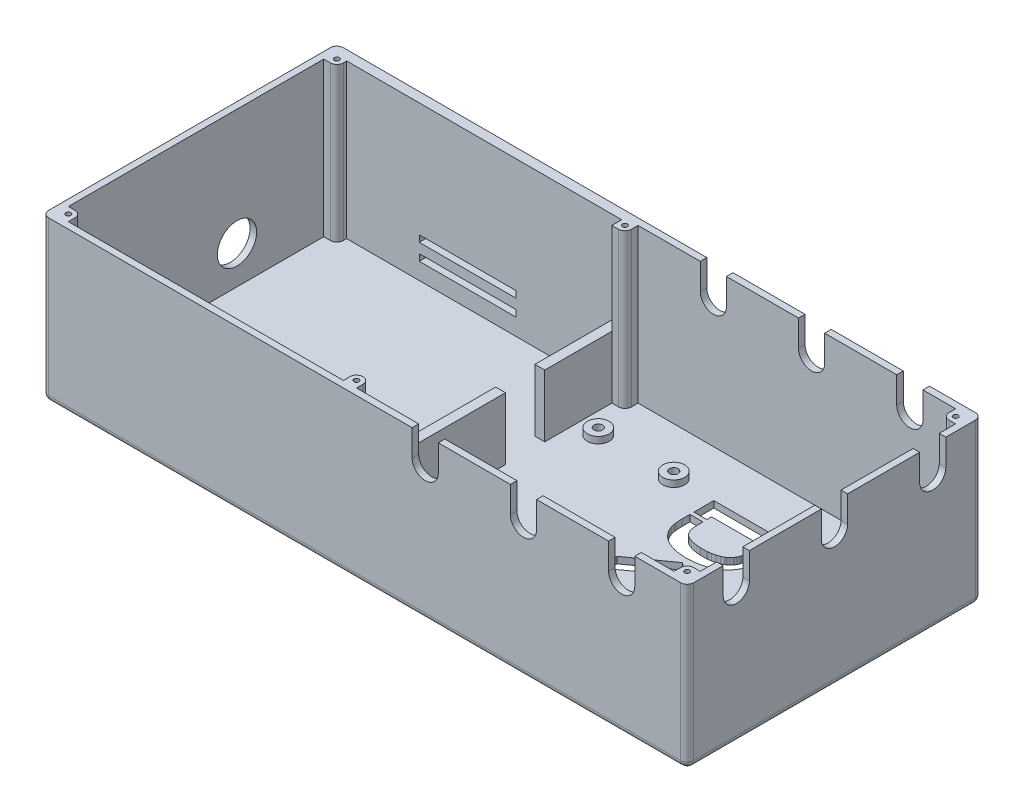
SolidWorks part; units mm, degrees
ref_plane "Front Plane" through (0, 0, 0) normal (0, 0, 1) x (1, 0, 0)
ref_plane "Top Plane" through (0, 0, 0) normal (0, 1, 0) x (1, 0, 0)
ref_plane "Right Plane" through (0, 0, 0) normal (1, 0, 0) x (0, 0, -1)
sketch "Sketch2" plane through (0, 0, 0) normal (0, 1, 0) x (1, 0, 0)
  line L1 (0, 0) -> (197, 0)
  line L2 (0, 0) -> (0, 90)
  line L3 (0, 90) -> (197, 90)
  line L4 (197, 0) -> (197, 90)
  dimension "D1" = 197
  dimension "D2" = 90
extrude "Boss-Extrude1" add sketch "Sketch2" along normal blind 21
shell "Shell1" thickness 2
sketch "Sketch3" plane through (0.4867, 2, 38.6702) normal (0, 1, 0) x (1, 0, 0)
  circle A0 centre (118.949, 112.1395) radius 1.325
  circle A1 centre (118.949, 54.0895) radius 3.325
  circle A2 centre (95.899, 54.0895) radius 3.325
  circle A3 centre (95.899, 112.1395) radius 3.325
  circle A4 centre (118.949, 112.1395) radius 3.325
  circle A5 centre (95.899, 112.1395) radius 1.325
  circle A6 centre (95.899, 54.0895) radius 1.325
  circle A7 centre (118.949, 54.0895) radius 1.325
extrude "Boss-Extrude2" add sketch "Sketch3" along normal blind 2
sketch "Sketch6" plane through (0, 2, 0) normal (0, 1, 0) x (1, 0, 0)
  circle A0 centre (119.4356, 73.4693) radius 1.325 construction
  circle A1 centre (96.3856, 73.4693) radius 1.325
  circle A2 centre (96.3856, 73.4693) radius 1.325
  circle A3 centre (119.4356, 15.4193) radius 1.325 construction
  circle A4 centre (96.3856, 15.4193) radius 1.325 construction
  circle A5 centre (119.4356, 73.4693) radius 1.325
  circle A6 centre (119.4356, 15.4193) radius 1.325
  circle A7 centre (96.3856, 15.4193) radius 1.325
  dimension "D1" = 0
extrude "Cut-Extrude2" cut sketch "Sketch6" against normal through all
sketch "Sketch7" plane through (0, 0, 0) normal (-1, 0, 0) x (0, 0, 1)
  line L1 (-90, 10.5) -> (-83.6201, 10.5) construction
  line L2 (-90, 21) -> (-90, 0) construction
  circle A0 centre (-57.5, 13.5) radius 6
  dimension "D1" = 12
  dimension "D2" = 3
  dimension "D3" = 32.5
sketch "Sketch8" plane through (0, 2, 0) normal (0, 1, 0) x (1, 0, 0)
  line L0 (2, 88) -> (2, 2) construction
  line L1 (2, 28) -> (87, 28)
  line L2 (2, 45) -> (15.4419, 45) construction
  line L3 (2, 87) -> (87, 87)
  line L4 (87, 28) -> (87, 87)
  line L5 (2, 88) -> (2, 2) construction
  line L7 (2, 25) -> (90, 25)
  line L8 (90, 25) -> (90, 90)
  line L9 (2, 90) -> (90, 90)
  line L10 (2, 25) -> (2, 28)
  line L11 (2, 87) -> (2, 90)
  line L12 (197, 90) -> (0, 90) construction
  dimension "D1" = 59
  dimension "D2" = 0
  dimension "D3" = 85
  dimension "D4" = 3
extrude "Boss-Extrude3" add sketch "Sketch8" along normal up to surface (19 mm away) up to face at (98.5, 21, -45)
sketch "Sketch10" plane through (0, 21, 0) normal (0, 1, 0) x (1, 0, 0)
  line L0 (87, 57.5) -> (90, 57.5) construction
  line L2 (90, 25) -> (90, 88) construction
  line L3 (87, 87) -> (87, 28) construction
  line L4 (87, 51.5) -> (90, 51.5)
  line L5 (87, 51.5) -> (87, 63.5)
  line L6 (87, 63.5) -> (90, 63.5)
  line L7 (90, 51.5) -> (90, 63.5)
  line L8 (87, 28) -> (87, 87) construction
  line L9 (90, 25) -> (90, 88) construction
  dimension "D1" = 12
  dimension "D2" = 6
extrude "Cut-Extrude5" cut sketch "Sketch10" against normal up to surface (19 mm away) up to face at (119.4356, 2, -18.7443)
sketch "Sketch12" plane through (0, 0, -75) normal (0, 0, -1) x (-1, 0, 0)
  line L1 (-57.7754, 12.1097) -> (-28.1833, 12.1097)
  line L2 (-57.7754, 12.1097) -> (-57.7754, 14.1097)
  line L3 (-57.7754, 14.1097) -> (-28.1833, 14.1097)
  line L4 (-28.1833, 12.1097) -> (-28.1833, 14.1097)
  line L5 (-57.7754, 7.1097) -> (-28.1833, 7.1097)
  line L6 (-57.7754, 7.1097) -> (-57.7754, 9.1097)
  line L7 (-57.7754, 9.1097) -> (-28.1833, 9.1097)
  line L8 (-28.1833, 7.1097) -> (-28.1833, 9.1097)
  dimension "D1" = 2
  dimension "D2" = 2
  dimension "D3" = 3
extrude "Cut-Extrude6" cut sketch "Sketch12" against normal up to surface (73 mm away) and the other way blind 67.0442 up to face at (98.5, 11.5, -2)
sketch "Sketch16" plane through (197, 0, 0) normal (1, 0, 0) x (0, 0, -1)
  line L0 (45, 21) -> (45, 0) construction
  line L1 (0, 21) -> (90, 21) construction
  line L2 (0, 0) -> (90, 0) construction
  line L3 (48, 14.2355) -> (48, 21)
  line L4 (48, 21) -> (42, 21)
  line L5 (42, 21) -> (42, 14.2355)
  arc A0 (42, 14.2355) -> (48, 14.2355) centre (45, 14.2355) ccw
  dimension "D1" = 6
extrude "Cut-Extrude8" cut sketch "Sketch16" against normal blind 10
fillet "Fillet1" radius 2 8 edges at (0, 10.5, -90) (197, 10.5, -90) (197, 10.5, 0) (197, 0, -45) (98.5, 0, -90) (0, 0, -45) (98.5, 0, 0) (0, 10.5, 0)
extrude "Cut-Extrude9" cut sketch "Sketch7" against normal blind 10
sketch "Sketch17" plane through (0, 21, 0) normal (0, 1, 0) x (1, 0, 0)
  line L0 (197, 48) -> (197, 42)
  line L22 (195, 90) -> (2, 90)
  line L23 (0, 88) -> (0, 2)
  line L24 (2, 0) -> (195, 0)
  line L25 (197, 2) -> (197, 42)
  line L27 (197, 42) -> (195, 42)
  line L28 (195, 42) -> (195, 2)
  line L29 (195, 2) -> (2, 2)
  line L30 (2, 2) -> (2, 25)
  line L31 (2, 25) -> (90, 25)
  line L32 (90, 25) -> (90, 51.5)
  line L33 (90, 51.5) -> (87, 51.5)
  line L34 (87, 51.5) -> (87, 28)
  line L35 (87, 28) -> (2, 28)
  line L36 (2, 28) -> (2, 87)
  line L37 (2, 87) -> (87, 87)
  line L38 (87, 87) -> (87, 63.5)
  line L39 (87, 63.5) -> (90, 63.5)
  line L40 (90, 63.5) -> (90, 88)
  line L41 (90, 88) -> (195, 88)
  line L42 (195, 88) -> (195, 48)
  line L43 (195, 48) -> (197, 48)
  line L44 (195, 90) -> (2, 90)
  line L45 (0, 88) -> (0, 2)
  line L46 (2, 0) -> (195, 0)
  line L47 (197, 2) -> (197, 42)
  line L48 (197, 48) -> (197, 88)
  line L49 (197, 48) -> (197, 88)
  arc A4 (2, 90) -> (0, 88) centre (2, 88) ccw
  arc A5 (0, 2) -> (2, 0) centre (2, 2) ccw
  arc A6 (195, 0) -> (197, 2) centre (195, 2) ccw
  arc A7 (197, 88) -> (195, 90) centre (195, 88) ccw
  arc A8 (2, 90) -> (0, 88) centre (2, 88) ccw
  arc A9 (0, 2) -> (2, 0) centre (2, 2) ccw
  arc A10 (195, 0) -> (197, 2) centre (195, 2) ccw
  arc A11 (197, 88) -> (195, 90) centre (195, 88) ccw
  dimension "D1" = 0
extrude "Boss-Extrude4" add sketch "Sketch17" along normal blind 24
sketch "Sketch18" plane through (0, 45, 0) normal (0, 1, 0) x (1, 0, 0)
  line L8 (194, 87) -> (3, 87)
  line L9 (3, 87) -> (3, 3)
  line L10 (3, 3) -> (194, 3)
  line L11 (194, 3) -> (194, 87)
  line L12 (194, 87) -> (3, 87)
  line L13 (3, 87) -> (3, 3)
  line L14 (3, 3) -> (194, 3)
  line L15 (194, 3) -> (194, 87)
  dimension "D1" = 3
extrude "Cut-Extrude10" cut sketch "Sketch18" against normal offset from surface (21 mm away) 3 up to face at (105, 21, -48.3333)
sketch "Sketch19" plane through (0, 2, 0) normal (0, 1, 0) x (1, 0, 0)
  line L0 (193, 88) -> (195, 88)
  line L1 (195, 88) -> (195, 84)
  line L2 (191, 86) -> (191, 88)
  line L3 (2, 2) -> (195, 2) construction
  line L4 (2, 25) -> (2, 2) construction
  line L5 (2, 2) -> (2, 88) construction
  line L6 (195, 90) -> (2, 90) construction
  line L7 (195, 2) -> (195, 88) construction
  line L8 (90, 63.5) -> (90, 88) construction
  line L9 (193, 84) -> (195, 84)
  line L10 (195, 88) -> (90, 88) construction
  line L11 (194, 45) -> (197, 45) construction
  line L12 (194, 3) -> (194, 87) construction
  line L13 (197, 2) -> (197, 88) construction
  line L14 (191, 2) -> (193, 2)
  line L15 (94, 4) -> (94, 2)
  line L16 (90, 4) -> (90, 2)
  line L17 (92, 84) -> (90, 84)
  line L18 (94, 86) -> (94, 88)
  line L19 (2, 88) -> (2, 84)
  line L20 (2, 88) -> (195, 88) construction
  line L21 (94, 88) -> (90, 88)
  line L22 (90, 84) -> (90, 88)
  line L23 (6, 4) -> (6, 2)
  line L24 (6, 2) -> (2, 2)
  line L25 (2, 2) -> (2, 6)
  line L26 (2, 6) -> (4, 6)
  line L27 (193, 6) -> (195, 6)
  line L28 (2, 84) -> (4, 84)
  line L29 (2, 88) -> (6, 88)
  line L30 (6, 88) -> (6, 86)
  line L31 (191, 88) -> (193, 88)
  line L32 (90, 2) -> (94, 2)
  line L33 (191, 4) -> (191, 2)
  line L34 (195, 2) -> (195, 6)
  line L35 (193, 2) -> (195, 2)
  arc A0 (6, 4) -> (4, 6) centre (4, 4) ccw
  arc A1 (4, 84) -> (6, 86) centre (4, 86) ccw
  arc A2 (191, 86) -> (193, 84) centre (193, 86) ccw
  arc A3 (191, 4) -> (193, 6) centre (193, 4) cw
  arc A4 (92, 84) -> (94, 86) centre (92, 86) ccw
  arc A5 (94, 4) -> (90, 4) centre (92, 4) ccw
  dimension "D1" = 2
  dimension "D2" = 2
  dimension "D3" = 4
  dimension "D6" = 4
  dimension "D7" = 4
  dimension "D9" = 4
  dimension "D4" = 2
  dimension "D5" = 4
  dimension "D8" = 2
  dimension "D10" = 2
extrude "Boss-Extrude5" add sketch "Sketch19" along direction (0, 1, 0) on the side of the normal up to surface (19 mm away)
sketch "Sketch22" plane through (0, 2, 0) normal (0, 1, 0) x (1, 0, 0)
  circle A0 centre (4, 4) radius 0.75
  circle A1 centre (4, 86) radius 0.75
  circle A2 centre (92, 86) radius 0.75
  circle A3 centre (193, 86) radius 0.75
  circle A4 centre (193, 4) radius 0.75
  circle A5 centre (92, 4) radius 0.75
  dimension "D1" = 1.5
  dimension "D2" = 1.5
  dimension "D3" = 1.5
  dimension "D4" = 1.5
  dimension "D5" = 1.5
  dimension "D6" = 1.5
extrude "Cut-Extrude11" cut sketch "Sketch22" along normal through all
sketch "Sketch23" plane through (0, 24, 0) normal (0, 1, 0) x (1, 0, 0)
  circle A0 centre (92, 4) radius 2
  circle A1 centre (4, 4) radius 2
  circle A2 centre (4, 86) radius 2
  circle A3 centre (92, 86) radius 2
  circle A4 centre (193, 86) radius 2
  circle A5 centre (181, 4) radius 2
  dimension "D1" = 4
  dimension "D2" = 4
  dimension "D3" = 4
  dimension "D4" = 4
  dimension "D5" = 4
  dimension "D6" = 4
extrude "Cut-Extrude12" cut sketch "Sketch23" along normal through all
sketch "Sketch24" plane through (0, 0, 0) normal (0, 0, 1) x (1, 0, 0)
  line L0 (197, 45) -> (197, 2) construction
  line L1 (0, 45) -> (197, 45)
  line L2 (0, 45) -> (0, 21)
  line L3 (0, 21) -> (197, 21)
  line L4 (197, 45) -> (197, 21)
  dimension "D1" = 24
extrude "Cut-Extrude13" cut sketch "Sketch24" against normal through all
sketch "Sketch25" plane through (0, 21, 0) normal (0, 1, 0) x (1, 0, 0)
  line L0 (2, 25) -> (2, 28)
  line L1 (90, 84) -> (90, 87)
  line L2 (90, 87) -> (87, 87)
  line L3 (195, 42) -> (195, 48)
  line L4 (197, 42) -> (197, 48)
  line L35 (197, 2) -> (197, 42)
  line L36 (197, 42) -> (195, 42)
  line L37 (195, 42) -> (195, 6)
  line L38 (195, 6) -> (193, 6)
  line L39 (191, 4) -> (191, 2)
  line L40 (191, 2) -> (94, 2)
  line L41 (94, 2) -> (94, 4)
  line L42 (90, 4) -> (90, 2)
  line L43 (90, 2) -> (6, 2)
  line L44 (6, 2) -> (6, 4)
  line L45 (4, 6) -> (2, 6)
  line L46 (2, 6) -> (2, 25)
  line L47 (2, 25) -> (90, 25)
  line L48 (90, 25) -> (90, 51.5)
  line L49 (90, 51.5) -> (87, 51.5)
  line L50 (87, 51.5) -> (87, 28)
  line L51 (87, 28) -> (2, 28)
  line L52 (2, 28) -> (2, 84)
  line L53 (2, 84) -> (4, 84)
  line L54 (6, 86) -> (6, 87)
  line L55 (6, 87) -> (87, 87)
  line L56 (87, 87) -> (87, 63.5)
  line L57 (87, 63.5) -> (90, 63.5)
  line L58 (90, 63.5) -> (90, 84)
  line L59 (90, 84) -> (92, 84)
  line L60 (94, 86) -> (94, 88)
  line L61 (94, 88) -> (191, 88)
  line L62 (191, 88) -> (191, 86)
  line L63 (193, 84) -> (195, 84)
  line L64 (195, 84) -> (195, 48)
  line L65 (195, 48) -> (197, 48)
  line L66 (197, 48) -> (197, 88)
  line L67 (195, 90) -> (2, 90)
  line L68 (0, 88) -> (0, 2)
  line L69 (2, 0) -> (195, 0)
  line L70 (197, 2) -> (197, 42)
  line L72 (195, 42) -> (195, 6)
  line L73 (195, 6) -> (193, 6)
  line L74 (191, 4) -> (191, 2)
  line L75 (191, 2) -> (94, 2)
  line L76 (94, 2) -> (94, 4)
  line L77 (90, 4) -> (90, 2)
  line L78 (90, 2) -> (6, 2)
  line L79 (6, 2) -> (6, 4)
  line L80 (4, 6) -> (2, 6)
  line L81 (2, 6) -> (2, 25)
  line L87 (2, 28) -> (2, 84)
  line L88 (2, 84) -> (4, 84)
  line L89 (6, 86) -> (6, 87)
  line L90 (6, 87) -> (87, 87)
  line L94 (90, 84) -> (92, 84)
  line L95 (94, 86) -> (94, 88)
  line L96 (94, 88) -> (191, 88)
  line L97 (191, 88) -> (191, 86)
  line L98 (193, 84) -> (195, 84)
  line L99 (195, 84) -> (195, 48)
  line L101 (197, 48) -> (197, 88)
  line L102 (195, 90) -> (2, 90)
  line L103 (0, 88) -> (0, 2)
  line L104 (2, 0) -> (195, 0)
  circle A0 centre (4, 4) radius 0.75 construction
  circle A1 centre (4, 86) radius 0.75 construction
  circle A2 centre (92, 86) radius 0.75 construction
  circle A3 centre (193, 86) radius 0.75 construction
  circle A4 centre (193, 4) radius 0.75 construction
  circle A5 centre (92, 4) radius 0.75 construction
  circle A6 centre (4, 4) radius 0.75
  circle A7 centre (4, 86) radius 0.75
  circle A8 centre (92, 86) radius 0.75
  circle A9 centre (193, 86) radius 0.75
  arc A10 (195, 0) -> (197, 2) centre (195, 2) ccw
  arc A11 (193, 6) -> (191, 4) centre (193, 4) ccw
  arc A12 (94, 4) -> (90, 4) centre (92, 4) ccw
  arc A13 (6, 4) -> (4, 6) centre (4, 4) ccw
  arc A14 (4, 84) -> (6, 86) centre (4, 86) ccw
  arc A15 (92, 84) -> (94, 86) centre (92, 86) ccw
  arc A16 (191, 86) -> (193, 84) centre (193, 86) ccw
  arc A17 (197, 88) -> (195, 90) centre (195, 88) ccw
  arc A18 (2, 90) -> (0, 88) centre (2, 88) ccw
  arc A19 (0, 2) -> (2, 0) centre (2, 2) ccw
  arc A20 (195, 0) -> (197, 2) centre (195, 2) ccw
  arc A21 (193, 6) -> (191, 4) centre (193, 4) ccw
  arc A22 (94, 4) -> (90, 4) centre (92, 4) ccw
  arc A23 (6, 4) -> (4, 6) centre (4, 4) ccw
  arc A24 (4, 84) -> (6, 86) centre (4, 86) ccw
  arc A25 (92, 84) -> (94, 86) centre (92, 86) ccw
  arc A26 (191, 86) -> (193, 84) centre (193, 86) ccw
  arc A27 (197, 88) -> (195, 90) centre (195, 88) ccw
  arc A28 (2, 90) -> (0, 88) centre (2, 88) ccw
  arc A29 (0, 2) -> (2, 0) centre (2, 2) ccw
  circle A30 centre (193, 4) radius 0.75
  circle A31 centre (92, 4) radius 0.75
  dimension "D1" = 0
extrude "Boss-Extrude9" add sketch "Sketch25" along normal blind 28
sketch "Sketch26" plane through (197, 0, 0) normal (1, 0, 0) x (0, 0, -1)
  line L0 (48, 21) -> (42, 21)
  line L1 (42, 21) -> (42, 14.2355)
  line L2 (48, 14.2355) -> (48, 21)
  arc A0 (42, 14.2355) -> (48, 14.2355) centre (45, 14.2355) ccw
extrude "Boss-Extrude10" add sketch "Sketch26" against normal up to surface (2 mm away)
sketch "Sketch27" plane through (0, 49, 0) normal (0, 1, 0) x (1, 0, 0)
  line L0 (197, 2) -> (197, 88) construction
  line L1 (195, 90) -> (2, 90) construction
  line L2 (2, 0) -> (195, 0) construction
  line L3 (0, 88) -> (0, 2) construction
  line L4 (197, 2) -> (197, 88)
  line L5 (195, 90) -> (2, 90)
  line L6 (2, 0) -> (195, 0)
  line L7 (0, 88) -> (0, 2)
  arc A0 (195, 0) -> (197, 2) centre (195, 2) ccw construction
  arc A1 (197, 88) -> (195, 90) centre (195, 88) ccw construction
  arc A2 (2, 90) -> (0, 88) centre (2, 88) ccw construction
  arc A3 (0, 2) -> (2, 0) centre (2, 2) ccw construction
  arc A4 (195, 0) -> (197, 2) centre (195, 2) ccw
  arc A5 (197, 88) -> (195, 90) centre (195, 88) ccw
  arc A6 (2, 90) -> (0, 88) centre (2, 88) ccw
  arc A7 (0, 2) -> (2, 0) centre (2, 2) ccw
extrude "Boss-Extrude11" add sketch "Sketch27" along normal blind 30
sketch "Sketch28" plane through (0, 79, 0) normal (0, 1, 0) x (1, 0, 0)
  line L8 (194, 3) -> (194, 87)
  line L9 (194, 87) -> (3, 87)
  line L10 (3, 87) -> (3, 3)
  line L11 (3, 3) -> (194, 3)
  line L12 (194, 3) -> (194, 87)
  line L13 (194, 87) -> (3, 87)
  line L14 (3, 87) -> (3, 3)
  line L15 (3, 3) -> (194, 3)
  dimension "D1" = 3
extrude "Cut-Extrude14" cut sketch "Sketch28" against normal blind 27
sketch "Sketch29" plane through (0, 2, 0) normal (0, 1, 0) x (1, 0, 0)
  circle A0 centre (4, 4) radius 0.75 construction
  circle A1 centre (4, 86) radius 0.75 construction
  circle A2 centre (193, 86) radius 0.75 construction
  circle A3 centre (193, 4) radius 0.75 construction
  circle A4 centre (92, 4) radius 0.75 construction
  circle A5 centre (92, 86) radius 0.75 construction
  circle A6 centre (4, 4) radius 0.75
  circle A7 centre (4, 86) radius 0.75
  circle A8 centre (193, 86) radius 0.75
  circle A9 centre (193, 4) radius 0.75
  circle A10 centre (92, 4) radius 0.75
  circle A11 centre (92, 86) radius 0.75
extrude "Cut-Extrude15" cut sketch "Sketch29" along normal through all
sketch "Sketch30" plane through (0, 0, 0) normal (0, 0, 1) x (1, 0, 0)
  line L0 (197, 79) -> (197, 2) construction
  line L1 (0, 79) -> (197, 79)
  line L2 (0, 79) -> (0, 49)
  line L3 (0, 49) -> (197, 49)
  line L4 (197, 79) -> (197, 49)
  dimension "D1" = 30
extrude "Cut-Extrude16" cut sketch "Sketch30" against normal through all
sketch "Sketch31" plane through (197, 0, 0) normal (1, 0, 0) x (0, 0, -1)
  line L0 (45, 49) -> (45, 0) construction
  line L1 (88, 49) -> (2, 49) construction
  line L2 (88, 0) -> (2, 0) construction
  line L3 (11, 41) -> (11, 49)
  line L4 (11, 49) -> (19, 49)
  line L5 (19, 49) -> (19, 41)
  line L6 (41, 41) -> (41, 49)
  line L7 (41, 49) -> (49, 49)
  line L8 (49, 49) -> (49, 41)
  line L9 (71, 41) -> (71, 49)
  line L10 (71, 49) -> (79, 49)
  line L11 (79, 49) -> (79, 41)
  arc A0 (41, 41) -> (49, 41) centre (45, 41) ccw
  arc A1 (71, 41) -> (79, 41) centre (75, 41) ccw
  arc A2 (11, 41) -> (19, 41) centre (15, 41) ccw
  dimension "D1" = 8
  dimension "D2" = 8
  dimension "D3" = 8
  dimension "D4" = 30
  dimension "D5" = 30
  dimension "D6" = 8
  dimension "D7" = 8
  dimension "D8" = 8
extrude "Cut-Extrude17" cut sketch "Sketch31" against normal blind 10
sketch "Sketch32" plane through (0, 0, -90) normal (0, 0, -1) x (-1, 0, 0)
  line L0 (-197, 2) -> (-197, 49) construction
  line L1 (-2, 49) -> (-195, 49) construction
  line L2 (-181, 41) -> (-181, 49)
  line L3 (-181, 49) -> (-173, 49)
  line L4 (-173, 49) -> (-173, 41)
  line L5 (-151, 41) -> (-151, 49)
  line L6 (-151, 49) -> (-143, 49)
  line L7 (-143, 49) -> (-143, 41)
  line L8 (-121, 41) -> (-121, 49)
  line L9 (-121, 49) -> (-113, 49)
  line L10 (-113, 49) -> (-113, 41)
  arc A0 (-181, 41) -> (-173, 41) centre (-177, 41) ccw
  arc A1 (-151, 41) -> (-143, 41) centre (-147, 41) ccw
  arc A2 (-121, 41) -> (-113, 41) centre (-117, 41) ccw
  dimension "D1" = 8
  dimension "D2" = 8
  dimension "D3" = 8
  dimension "D4" = 20
  dimension "D5" = 30
  dimension "D6" = 30
  dimension "D7" = 8
  dimension "D8" = 8
  dimension "D9" = 8
extrude "Cut-Extrude18" cut sketch "Sketch32" against normal through all
sketch "Sketch33" plane through (0, 0, 0) normal (0, -1, 0) x (1, 0, 0)
  line L0 (157, -90) -> (157, 0) construction
  line L1 (195, -90) -> (2, -90) construction
  line L2 (2, 0) -> (195, 0) construction
  line L3 (197, -2) -> (197, -88) construction
  line L4 (131.3421, -73.8037) -> (154.2999, -73.8037)
  line L5 (154.2999, -73.8037) -> (154.2997, -67.6994)
  line L6 (154.2997, -67.6994) -> (150.3165, -67.6995)
  line L7 (150.3165, -67.6995) -> (150.3163, -69.1497)
  line L8 (150.3163, -69.1497) -> (135.3192, -69.1478)
  line L9 (135.3192, -69.1478) -> (135.3192, -67.6999)
  line L10 (135.3192, -67.6999) -> (131.3412, -67.7)
  line L11 (131.3412, -67.7) -> (131.3421, -73.8037)
  line L12 (131.3412, -66.4846) -> (135.3193, -66.4846)
  line L13 (135.3193, -66.4846) -> (135.3437, -64.4481)
  line L14 (150.3168, -66.4847) -> (154.2999, -66.4847)
  line L15 (154.2999, -66.4847) -> (154.3061, -63.8278)
  line L16 (142.9536, -52.5566) -> (154.2999, -44.6163)
  line L17 (154.2999, -44.6163) -> (154.3013, -38.4291)
  line L18 (154.3013, -38.4291) -> (142.9749, -46.7185)
  line L19 (142.9749, -46.7185) -> (131.3435, -38.1748)
  line L20 (131.3435, -38.1748) -> (131.3413, -44.2952)
  line L21 (131.3413, -44.2952) -> (142.9536, -52.5566)
  line L22 (135.4022, -35.8458) -> (131.3413, -35.8456)
  line L23 (131.3426, -16.3948) -> (135.4036, -16.3948)
  line L24 (135.4036, -16.3948) -> (135.4022, -35.8458)
  line L25 (131.3413, -35.8456) -> (131.3426, -16.3948)
  line L26 (140.9135, -35.8453) -> (140.9135, -16.3948)
  line L27 (140.9135, -16.3948) -> (144.9826, -16.3975)
  line L28 (144.9826, -16.3975) -> (144.9811, -35.8432)
  line L29 (144.9811, -35.8432) -> (140.9135, -35.8453)
  line L30 (150.2258, -35.8453) -> (150.2258, -16.3948)
  line L31 (150.2258, -16.3948) -> (154.3061, -16.3948)
  line L32 (154.3061, -16.3948) -> (154.3061, -35.8456)
  line L33 (154.3061, -35.8456) -> (150.2258, -35.8453)
  line L34 (131.3412, -66.4846) -> (131.3411, -64.0815)
  line L35 (135.3437, -64.4481) -> (135.3668, -63.9319)
  line L36 (135.3668, -63.9319) -> (135.5608, -62.7087)
  line L37 (135.5608, -62.7087) -> (135.6821, -62.3042)
  line L38 (135.6821, -62.3042) -> (135.8937, -61.8067)
  line L39 (135.8937, -61.8067) -> (136.2752, -61.1971)
  line L40 (136.2752, -61.1971) -> (136.7685, -60.6773)
  line L41 (136.7685, -60.6773) -> (137.2064, -60.3583)
  line L42 (137.2064, -60.3583) -> (137.3654, -60.277)
  line L43 (137.3654, -60.277) -> (137.6195, -60.1413)
  line L44 (137.6195, -60.1413) -> (138.4293, -59.8215)
  line L45 (138.4293, -59.8215) -> (139.5471, -59.5286)
  line L46 (139.5471, -59.5286) -> (140.6951, -59.358)
  line L47 (140.6951, -59.358) -> (141.5601, -59.285)
  line L48 (141.5601, -59.285) -> (141.849, -59.27)
  line L49 (141.849, -59.27) -> (142.008, -59.272)
  line L50 (142.008, -59.272) -> (142.8052, -59.2651)
  line L51 (142.8052, -59.2651) -> (143.601, -59.2905)
  line L52 (143.601, -59.2905) -> (143.7597, -59.3084)
  line L53 (143.7597, -59.3084) -> (144.051, -59.3297)
  line L54 (144.051, -59.3297) -> (144.9218, -59.4438)
  line L55 (144.9218, -59.4438) -> (146.0673, -59.6949)
  line L56 (146.0673, -59.6949) -> (147.1696, -60.0846)
  line L57 (147.1696, -60.0846) -> (147.6054, -60.3021)
  line L58 (147.6054, -60.3021) -> (147.9572, -60.4777)
  line L59 (147.9572, -60.4777) -> (148.2019, -60.6362)
  line L60 (148.2019, -60.6362) -> (148.3735, -60.747)
  line L61 (148.3735, -60.747) -> (148.8497, -61.1399)
  line L62 (148.8497, -61.1399) -> (149.3992, -61.7492)
  line L63 (149.3992, -61.7492) -> (149.8293, -62.4465)
  line L64 (149.8293, -62.4465) -> (150.0666, -63.0171)
  line L65 (150.0666, -63.0171) -> (150.1644, -63.3706)
  line L66 (150.1644, -63.3706) -> (150.2864, -64.1693)
  line L67 (150.2864, -64.1693) -> (150.3176, -64.9783)
  line L68 (150.3176, -64.9783) -> (150.3173, -65.1399)
  line L69 (150.3173, -65.1399) -> (150.317, -65.4742)
  line L70 (150.317, -65.4742) -> (150.3168, -66.4847)
  line L71 (131.3411, -64.0815) -> (131.4092, -62.5005)
  line L72 (131.4092, -62.5005) -> (131.4978, -61.8017)
  line L73 (131.4978, -61.8017) -> (131.5541, -61.4245)
  line L74 (131.5541, -61.4245) -> (131.7977, -60.4677)
  line L75 (131.7977, -60.4677) -> (132.2918, -59.2511)
  line L76 (132.2918, -59.2511) -> (132.9828, -58.1365)
  line L77 (132.9828, -58.1365) -> (133.6215, -57.3826)
  line L78 (133.6215, -57.3826) -> (133.8622, -57.1612)
  line L79 (133.8622, -57.1612) -> (134.1125, -56.9323)
  line L80 (134.1125, -56.9323) -> (134.9302, -56.3181)
  line L81 (134.9302, -56.3181) -> (136.106, -55.6332)
  line L82 (136.106, -55.6332) -> (137.3641, -55.1119)
  line L83 (137.3641, -55.1119) -> (138.3458, -54.8262)
  line L84 (138.3458, -54.8262) -> (138.6788, -54.7598)
  line L85 (138.6788, -54.7598) -> (138.7692, -54.7401)
  line L86 (138.7692, -54.7401) -> (139.6792, -54.5745)
  line L87 (139.6792, -54.5745) -> (139.961, -54.5364)
  line L88 (139.961, -54.5364) -> (140.4741, -54.4801)
  line L89 (140.4741, -54.4801) -> (141.8734, -54.3768)
  line L90 (141.8734, -54.3768) -> (142.4218, -54.3745)
  line L91 (142.4218, -54.3745) -> (143.4907, -54.4074)
  line L92 (143.4907, -54.4074) -> (144.9108, -54.5393)
  line L93 (144.9108, -54.5393) -> (146.3138, -54.7887)
  line L94 (146.3138, -54.7887) -> (147.3503, -55.0557)
  line L95 (147.3503, -55.0557) -> (147.6049, -55.1393)
  line L96 (147.6049, -55.1393) -> (147.6886, -55.1668)
  line L97 (147.6886, -55.1668) -> (147.9351, -55.249)
  line L98 (147.9351, -55.249) -> (148.6633, -55.5327)
  line L99 (148.6633, -55.5327) -> (149.606, -55.9763)
  line L100 (149.606, -55.9763) -> (150.5034, -56.5036)
  line L101 (150.5034, -56.5036) -> (151.1412, -56.9549)
  line L102 (151.1412, -56.9549) -> (151.3419, -57.12)
  line L103 (151.3419, -57.12) -> (151.5055, -57.2536)
  line L104 (151.5055, -57.2536) -> (151.9682, -57.6891)
  line L105 (151.9682, -57.6891) -> (152.5305, -58.3215)
  line L106 (152.5305, -58.3215) -> (153.0218, -59.0101)
  line L107 (153.0218, -59.0101) -> (153.3425, -59.5585)
  line L108 (153.3425, -59.5585) -> (153.4351, -59.7482)
  line L109 (153.4351, -59.7482) -> (153.5523, -59.9914)
  line L110 (153.5523, -59.9914) -> (153.8404, -60.7522)
  line L111 (153.8404, -60.7522) -> (154.1164, -61.799)
  line L112 (154.1164, -61.799) -> (154.2689, -62.8716)
  line L113 (154.2689, -62.8716) -> (154.3061, -63.6232)
  line L114 (154.3061, -63.6232) -> (154.3091, -63.6832)
  line L115 (154.3091, -63.6832) -> (154.3061, -63.8278)
  line L116 (2, -45) -> (195, -45) construction
  line L117 (2, -2) -> (2, -88) construction
  line L118 (195, -88) -> (195, -2) construction
  dimension "D1" = 40
extrude "Cut-Extrude19" cut sketch "Sketch33" against normal blind 10
